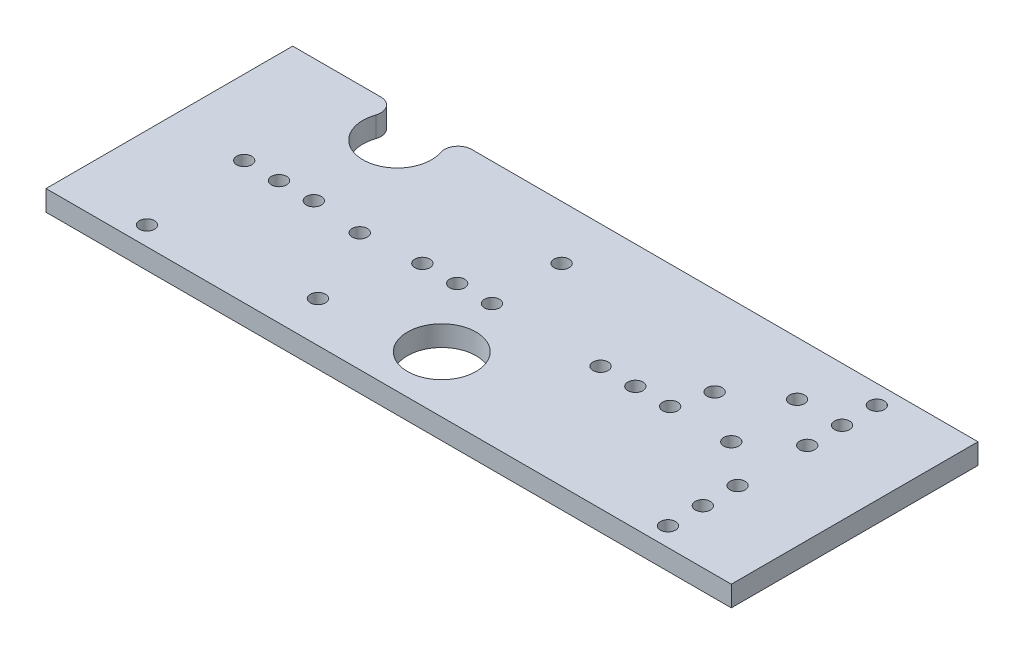
SolidWorks part; units mm, degrees
ref_plane "Front Plane" through (0, 0, 0) normal (0, 0, 1) x (1, 0, 0)
ref_plane "Top Plane" through (0, 0, 0) normal (0, 1, 0) x (1, 0, 0)
ref_plane "Right Plane" through (0, 0, 0) normal (1, 0, 0) x (0, 0, -1)
sketch "Sketch1" plane through (0, 0, 0) normal (0, 1, 0) x (1, 0, 0)
  line L1 (-25, -9) -> (25, -9)
  line L2 (-25, -9) -> (-25, 9)
  line L3 (-25, 9) -> (25, 9)
  line L4 (25, -9) -> (25, 9)
  line L5 (-25, -9) -> (25, 9) construction
  line L6 (-25, 9) -> (25, -9) construction
  point P0 (0, 0)
  dimension "D1" = 50
  dimension "D2" = 18
extrude "Boss-Extrude1" add sketch "Sketch1" along normal blind 1.5
sketch "Sketch2" plane through (0, 1.5, 0) normal (0, 1, 0) x (1, 0, 0)
  circle A0 centre (-15.25, 6.875) radius 2.5
  circle A1 centre (-0.25, -4.875) radius 2.5
  dimension "D1" = 5
  dimension "D2" = 5
extrude "Cut-Extrude1" cut sketch "Sketch2" against normal blind 10
sketch "Sketch3" plane through (0, 0, 0) normal (0, -1, 0) x (1, 0, 0)
  line L0 (-21.75, -2.375) -> (-12.25, 2.375) construction
  line L1 (-12.25, 2.375) -> (-8.75, -2.375) construction
  line L2 (-8.75, -2.375) -> (0.75, 2.375) construction
  line L3 (0.75, 2.375) -> (4.25, -2.375) construction
  line L4 (4.25, -2.375) -> (13.75, 2.375) construction
  line L5 (-21.75, 0) -> (13.75, 0) construction
  line L6 (-21.75, -2.375) -> (-21.75, 2.375) construction
  line L7 (13.75, -2.375) -> (13.75, 2.375) construction
  circle A0 centre (-17, 0) radius 0.55
  circle A1 centre (-4, 0) radius 0.55
  circle A2 centre (9, 0) radius 0.55
  circle A3 centre (-19.54, 0) radius 0.55
  circle A4 centre (-14.46, 0) radius 0.55
  circle A5 centre (-6.54, 0) radius 0.55
  circle A6 centre (-1.46, 0) radius 0.55
  circle A7 centre (6.46, 0) radius 0.55
  circle A8 centre (11.54, 0) radius 0.55
  dimension "D7" = 1.1
  dimension "D1" = 2.54
  dimension "D2" = 2.54
  dimension "D3" = 2.54
  dimension "D4" = 2.54
  dimension "D5" = 2.54
  dimension "D6" = 2.54
extrude "Cut-Extrude2" cut sketch "Sketch3" against normal through all
sketch "Sketch4" plane through (0, 1.5, 0) normal (0, 1, 0) x (1, 0, 0)
  line L0 (19, 9) -> (19, -9) construction
  line L1 (25, 9) -> (-13.933, 9) construction
  line L2 (-25, -9) -> (25, -9) construction
  line L3 (25, -9) -> (25, 9) construction
  circle A0 centre (19, 0) radius 0.55
  circle A1 centre (19, -2.54) radius 0.55
  circle A2 centre (19, -5.08) radius 0.55
  circle A3 centre (19, -7.62) radius 0.55
  circle A4 centre (19, 2.54) radius 0.55
  circle A5 centre (19, 5.08) radius 0.55
  circle A6 centre (19, 7.62) radius 0.55
  circle A7 centre (16, 0) radius 0.55
  dimension "D8" = 1.1
  dimension "D1" = 2.54
  dimension "D2" = 2.54
  dimension "D3" = 2.54
  dimension "D4" = 2.54
  dimension "D5" = 2.54
  dimension "D6" = 2.54
  dimension "D7" = 6
  dimension "D9" = 3
extrude "Cut-Extrude3" cut sketch "Sketch4" against normal through all contours L0 A6 | A6 L0 | L0 A5 | A5 L0 | L0 A4 | A4 L0 | A7 | L0 A1 | A1 L0 | A2 | A3
sketch "Sketch6" plane through (0, 1.5, 0) normal (0, 1, 0) x (1, 0, 0)
  line L0 (11.54, 0) -> (16, 0)
  line L1 (6.46, 0) -> (6.46, 2.54)
  line L2 (6.46, 2.54) -> (-4, 2.54)
  line L3 (-4, 2.54) -> (-4, 0)
  line L4 (-10.7569, -0.3523) -> (-19.014, -7.62) construction
  line L5 (-19.014, -7.62) -> (-8.1291, -6.0331) construction
  line L6 (-14.46, 0) -> (-4.4535, 5.08)
  line L7 (19, -2.54) -> (19, 2.54)
  line L8 (-8.1291, -6.0331) -> (-1.46, 0)
  line L9 (19, -5.08) -> (21.2576, -5.08)
  line L10 (21.2576, -5.08) -> (21.2576, 5.08)
  line L11 (21.2576, 5.08) -> (19, 5.08)
  line L12 (19, -7.62) -> (23.1258, -7.62)
  line L13 (23.1258, -7.62) -> (23.1258, 7.62)
  line L14 (23.1258, 7.62) -> (19, 7.62)
  line L15 (-10.7569, -0.3523) -> (-6.54, 0)
  line L16 (-19.54, 0) -> (-19.54, 1.1229)
  line L17 (-19.54, 1.1229) -> (-4.4535, 7.62)
  line L18 (-4.4535, 7.62) -> (19, 7.62)
  line L19 (9, -1.7591) -> (5.46, -1.7591)
  line L20 (19, 5.08) -> (15.7178, 5.08)
  line L21 (-4.4535, 5.08) -> (-1.46, 5.08)
  line L22 (-1.46, 5.08) -> (15.7178, 5.08) construction
  line L23 (9, 0) -> (9, -1.7591)
  line L24 (19, 2.54) -> (12.244, 2.54)
  line L25 (12.244, 2.54) -> (16.46, -7.62) construction
  line L26 (11.54, 0) -> (11.54, -2.0156)
  line L27 (-19.014, -7.62) -> (-20.7614, -3.8272)
  line L28 (-19.014, -7.62) -> (7.96, -7.62)
  line L29 (7.96, -7.62) -> (7.96, -5.1718)
  line L30 (5.46, -1.7591) -> (5.46, -5.1718)
  line L31 (11.54, -2.0156) -> (10.46, -2.0156)
  line L32 (10.46, -2.0156) -> (10.46, -5.1718)
  line L33 (16.46, -7.62) -> (12.96, -7.62)
  line L34 (12.96, -7.62) -> (12.96, -5.1718)
  line L35 (-20.7614, -3.8272) -> (-17, 0)
  circle A0 centre (5.46, -5.1718) radius 1 construction
  point P48 (11.54, -2.0156)
  point P55 (7.96, -5.1718)
  point P56 (-19.54, 1.1229)
  dimension "D9" = 2
  dimension "D1" = 11
  dimension "D2" = 2.54
  dimension "D3" = 11
  dimension "D4" = 11
  dimension "D5" = 2.5
  dimension "D6" = 2.5
  dimension "D7" = 2.5
  dimension "D8" = 3.5
sketch "Sketch8" plane through (0, 1.5, 0) normal (0, 1, 0) x (1, 0, 0)
  circle A0 centre (-10.7569, -0.3523) radius 0.55
  circle A1 centre (-8.1291, -6.0331) radius 0.55
  circle A2 centre (-19.014, -7.62) radius 0.55
  circle A3 centre (-1.46, 5.08) radius 0.55
  circle A4 centre (12.244, 2.54) radius 0.55
  circle A5 centre (15.7178, 5.08) radius 0.55
  circle A6 centre (-14.46, 0) radius 0.55 construction
extrude "Cut-Extrude5" cut sketch "Sketch8" against normal through all
sketch "Sketch9" plane through (0, 1.5, 0) normal (0, 1, 0) x (1, 0, 0)
  line L0 (5.46, -5.1718) -> (7.96, -5.1718) construction
  line L1 (7.96, -5.1718) -> (10.46, -5.1718) construction
  line L2 (10.46, -5.1718) -> (12.96, -5.1718) construction
  line L3 (12.96, -5.1718) -> (14.21, -5.1718) construction
  line L4 (5.46, -5.1718) -> (4.21, -5.1718) construction
  line L5 (4.21, -2.7885) -> (4.21, -6.6847)
  line L6 (4.21, -6.6847) -> (6.71, -6.6847)
  line L7 (6.71, -6.6847) -> (6.71, -5.1718)
  line L8 (6.71, -5.1718) -> (6.71, -2.7885)
  line L9 (6.71, -2.7885) -> (9.21, -2.7885)
  line L10 (9.21, -2.7885) -> (9.21, -5.1718)
  line L11 (9.21, -5.1718) -> (9.21, -7.6371)
  line L12 (9.21, -7.6371) -> (11.71, -7.6371)
  line L13 (11.71, -7.6371) -> (11.71, -5.1718)
  line L14 (11.71, -5.1718) -> (11.71, -2.9597)
  line L15 (11.71, -2.9597) -> (14.21, -2.9597)
  line L16 (14.21, -2.9597) -> (14.21, -5.1718)
  line L17 (14.21, -5.1718) -> (14.21, -6.4499)
  point P14 (6.71, -6.6847)
  point P24 (9.21, -2.7789)
  point P25 (11.71, -7.6371)
  point P26 (14.6338, -2.7192)
  point P27 (14.07, -6.4499)
  point P28 (14.21, -2.9597)
  point P29 (4.21, -2.7885)
  dimension "D1" = 2.5
  dimension "D2" = 1.25
fillet "Fillet2" radius 1 2 edges at (-16.567, 0.75, -9) (-13.933, 0.75, -9)
